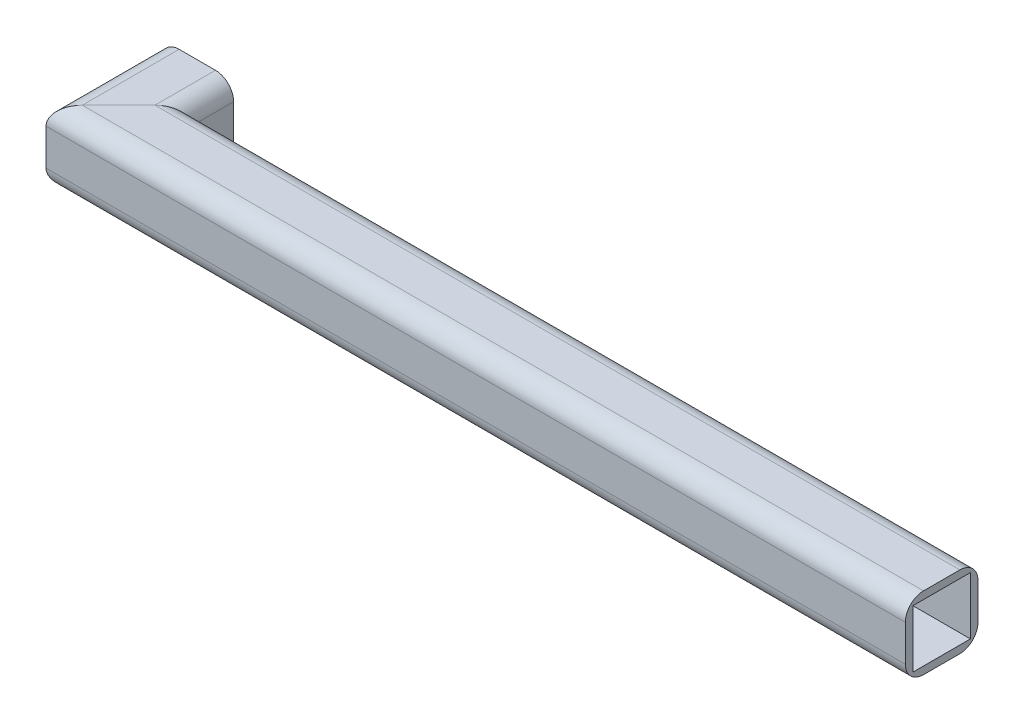
SolidWorks part; units mm, degrees
ref_plane "Front Plane" through (0, 0, 0) normal (0, 0, 1) x (1, 0, 0)
ref_plane "Top Plane" through (0, 0, 0) normal (0, 1, 0) x (1, 0, 0)
ref_plane "Right Plane" through (0, 0, 0) normal (1, 0, 0) x (0, 0, -1)
sketch3d "3DSketch3"
  line L0 (60.325, 60.325, 0) -> (60.325, 60.325, 165.1)
  line L5 (60.325, 60.325, 165.1) -> (1787.525, 60.325, 165.1)
  dimension "D3" = 165.1
  dimension "D4" = 1727.2
sketch "Sketch12" plane through (0, 0, 0) normal (0, 0, 1) x (1, 0, 0)
  line L0 (120.65, 0) -> (120.65, 120.65)
  line L6 (22.225, 136.525) -> (98.425, 136.525)
  line L7 (120.65, 120.65) -> (0, 120.65)
  line L8 (0, 120.65) -> (0, 0)
  line L9 (0, 0) -> (120.65, 0)
  line L10 (-15.875, 98.425) -> (-15.875, 22.225)
  line L11 (22.225, -15.875) -> (98.425, -15.875)
  line L12 (136.525, 98.425) -> (136.525, 22.225)
  line L13 (-15.875, 136.525) -> (136.525, -15.875) construction
  line L14 (-15.875, -15.875) -> (136.525, 136.525) construction
  arc A7 (-15.875, 22.225) -> (22.225, -15.875) centre (22.225, 22.225) ccw
  arc A8 (98.425, -15.875) -> (136.525, 22.225) centre (98.425, 22.225) ccw
  arc A9 (98.425, 136.525) -> (136.525, 98.425) centre (98.425, 98.425) cw
  arc A10 (22.225, 136.525) -> (-15.875, 98.425) centre (22.225, 98.425) ccw
  point P0 (60.325, 60.325)
  point P6 (60.325, 60.325)
  dimension "D3" = 152.4
  dimension "D5" = 38.1
  dimension "D1" = 120.65
  dimension "D2" = 120.65
  dimension "D4" = 152.4
sweep "Sweep1" add profiles "Sketch12" path "3DSketch3"
